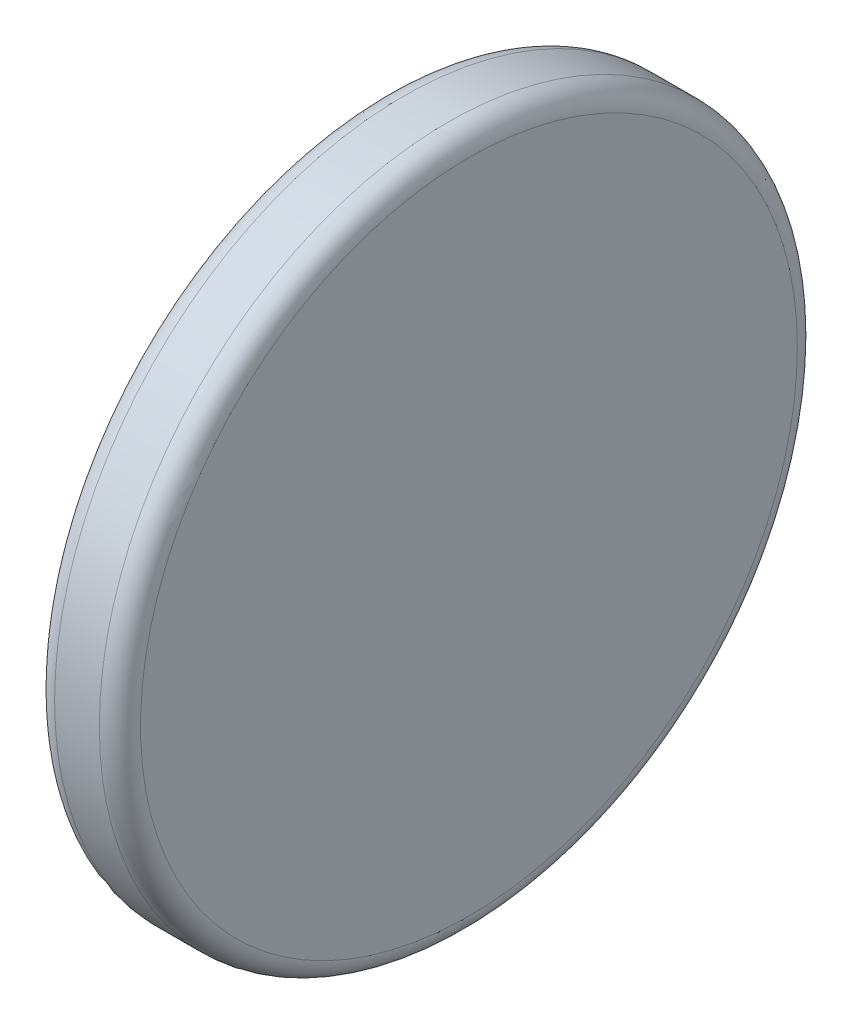
SolidWorks part; units mm, degrees
material "Rubber"
ref_plane "Front Plane" through (0, 0, 0) normal (0, 0, 1) x (1, 0, 0)
ref_plane "Top Plane" through (0, 0, 0) normal (0, 1, 0) x (1, 0, 0)
ref_plane "Right Plane" through (0, 0, 0) normal (1, 0, 0) x (0, 0, -1)
sketch "Sketch1" plane through (0, 0, 0) normal (1, 0, 0) x (0, 0, -1)
  circle A0 centre (0, 0) radius 203.2
  dimension "D1" = 406.4
extrude "Boss-Extrude1" add sketch "Sketch1" along normal mid plane 50
fillet "Fillet1" radius 12 2 edges at (-25, 0, -203.2) (25, 0, -203.2)
equation "\"tire_diameter\"= 16in"
equation "\"tire_width\"= 50mm"
equation "\"D1@Boss-Extrude1\"=\"tire_width\""
